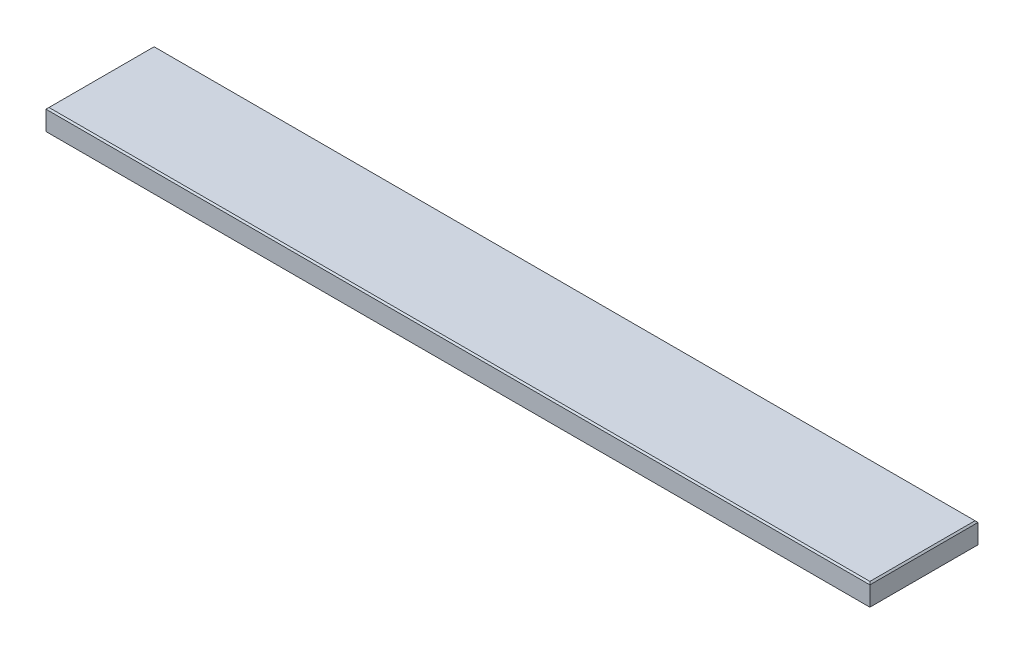
SolidWorks part; units mm, degrees
material "Oak"
ref_plane "Front Plane" through (0, 0, 0) normal (0, 0, 1) x (1, 0, 0)
ref_plane "Top Plane" through (0, 0, 0) normal (0, 1, 0) x (1, 0, 0)
ref_plane "Right Plane" through (0, 0, 0) normal (1, 0, 0) x (0, 0, -1)
sketch "Sketch1" plane through (0, 0, 0) normal (0, 1, 0) x (1, 0, 0)
  line L1 (0, 0) -> (1403.35, 0)
  line L2 (0, 0) -> (0, 184.15)
  line L3 (0, 184.15) -> (1403.35, 184.15)
  line L4 (1403.35, 0) -> (1403.35, 184.15)
  dimension "D1" = 184.15
  dimension "D2" = 1403.35
extrude "Boss-Extrude1" add sketch "Sketch1" along normal blind 38.1
chamfer "Chamfer1" distance 2.54 angle 45 8 edges at (701.675, 38.1, 0) (0, 38.1, -92.075) (701.675, 38.1, -184.15) (1403.35, 38.1, -92.075) (701.675, 0, -184.15) (0, 0, -92.075) (701.675, 0, 0) (1403.35, 0, -92.075)
